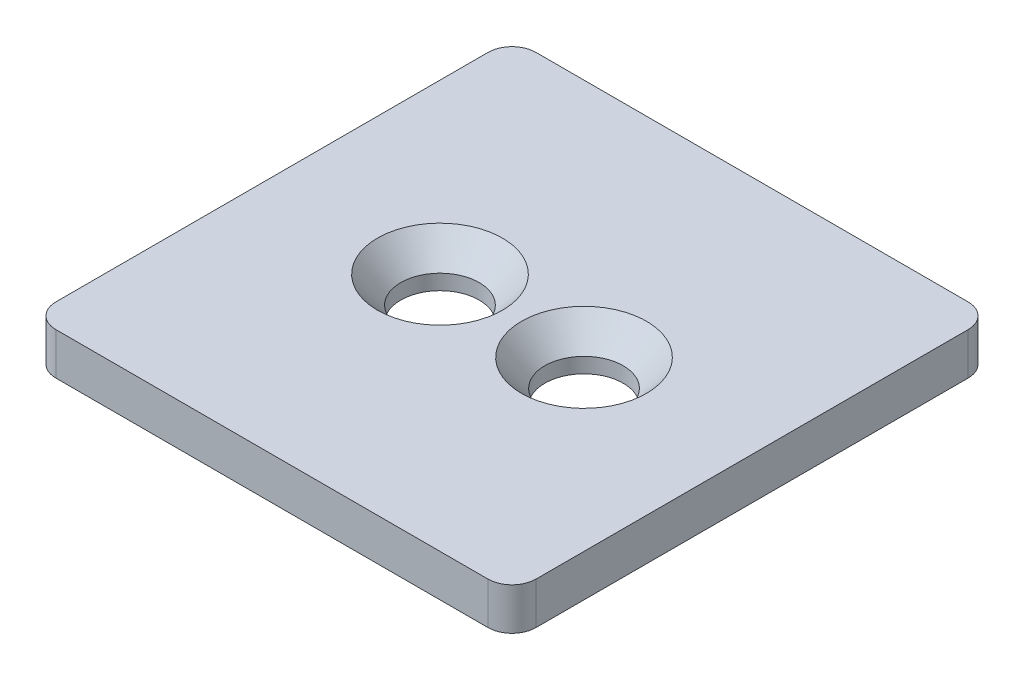
SolidWorks part; units mm, degrees
ref_plane "Front Plane" through (0, 0, 0) normal (0, 0, 1) x (1, 0, 0)
ref_plane "Top Plane" through (0, 0, 0) normal (0, 1, 0) x (1, 0, 0)
ref_plane "Right Plane" through (0, 0, 0) normal (1, 0, 0) x (0, 0, -1)
sketch "Sketch1" plane through (0, 0, 0) normal (0, 1, 0) x (1, 0, 0)
  line L1 (-10, -10) -> (10, -10)
  line L2 (-10, -10) -> (-10, 10)
  line L3 (-10, 10) -> (10, 10)
  line L4 (10, -10) -> (10, 10)
  line L5 (-10, -10) -> (10, 10) construction
  line L6 (-10, 10) -> (10, -10) construction
  point P0 (0, 0)
  dimension "D1" = 20
  dimension "D2" = 20
extrude "Boss-Extrude1" add sketch "Sketch1" along normal blind 1.75
sketch "Sketch3" plane through (0, 1.75, 0) normal (0, 1, 0) x (1, 0, 0)
  line L0 (0, 0) -> (-12.8331, 0) construction
  line L1 (0, -0.9625) -> (0, 0.9625) construction
  circle A0 centre (0, 0) radius 6 construction
  point P1 (-3, 0)
  point P7 (3, 0)
  dimension "D2" = 12
  dimension "D1" = 3
hole_wizard "CSK for #4 Flat Head Machine Screw1" positions "Sketch3" profile "Sketch4" countersink size "#4" standard "ANSI Inch" end condition through all
sketch "Sketch4" plane through (3, 1.75, 0) normal (1, 0, 0) x (0, 0, 1)
  line L0 (0, 0) -> (0, 1.75)
  line L1 (0, 1.75) -> (1.6319, 1.75)
  line L2 (1.6319, 1.75) -> (1.6319, 1.1176)
  line L3 (1.6319, 1.1176) -> (2.6035, 0)
  line L5 (2.6035, 0) -> (0, 0)
  line L6 (-1.632, 1.1176) -> (-2.6035, 0) construction
  line L11 (0, -6.35) -> (0, 107.95) construction
  dimension "Thru Hole Dia." = 3.2639
  dimension "Thru Hole Depth" = 1.75
  dimension "Near C'Sink Dia." = 5.207
  dimension "Near C'Sink Angle" = 82
fillet "Fillet2" radius 1 4 edges at (-10, 0.875, -10) (10, 0.875, -10) (10, 0.875, 10) (-10, 0.875, 10)
